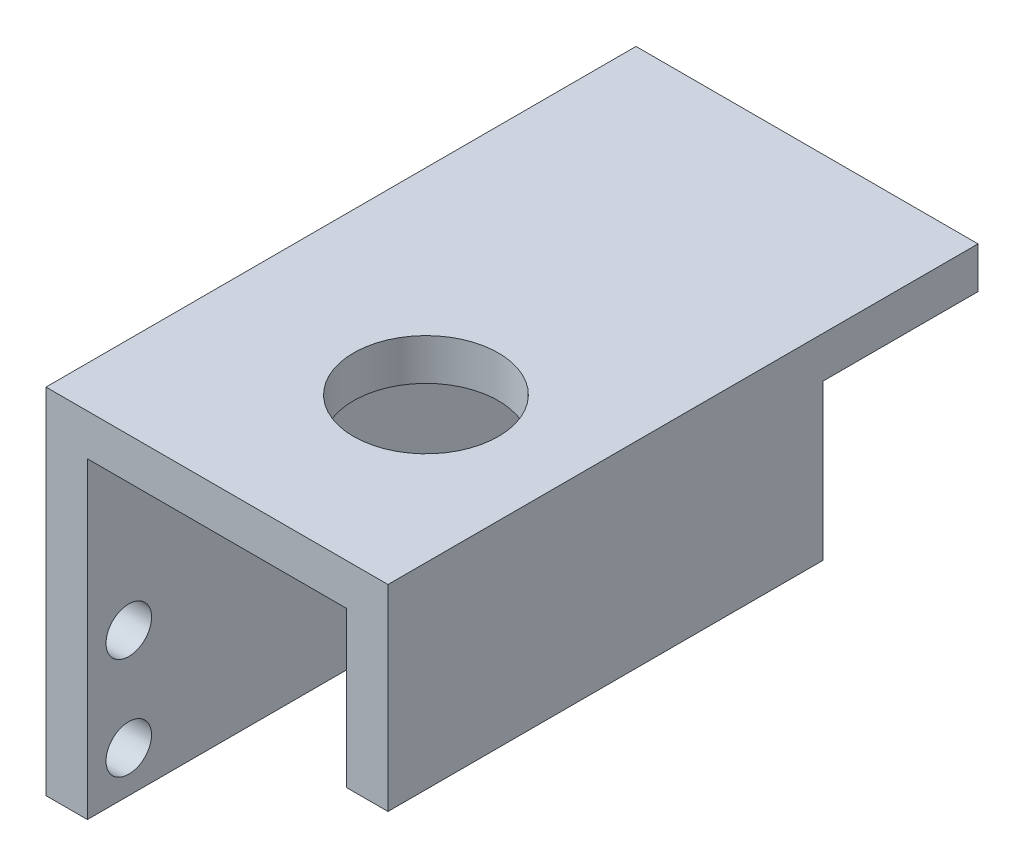
SolidWorks part; units mm, degrees
ref_plane "Front Plane" through (0, 0, 0) normal (0, 0, 1) x (1, 0, 0)
ref_plane "Top Plane" through (0, 0, 0) normal (0, 1, 0) x (1, 0, 0)
ref_plane "Right Plane" through (0, 0, 0) normal (1, 0, 0) x (0, 0, -1)
sketch "Sketch1" plane through (0, 0, 0) normal (1, 0, 0) x (0, 0, -1)
  line L1 (-28.51, 17.1) -> (28.51, 17.1)
  line L2 (-28.51, 17.1) -> (-28.51, -17.1)
  line L3 (-28.51, -17.1) -> (28.51, -17.1)
  line L4 (28.51, 17.1) -> (28.51, -17.1)
  line L5 (-28.51, 17.1) -> (28.51, -17.1) construction
  line L6 (-28.51, -17.1) -> (28.51, 17.1) construction
  circle A0 centre (-24.51, -3.25) radius 2.2
  circle A1 centre (-24.51, -13.1) radius 2.2
  circle A2 centre (24.51, -3.25) radius 2.2
  circle A3 centre (24.51, -13.1) radius 2.2
  point P0 (0, 0)
  dimension "D1" = 49.02
  dimension "D2" = 49.02
  dimension "D3" = 9.85
  dimension "D4" = 4.4
  dimension "D5" = 4.4
  dimension "D6" = 4.4
  dimension "D7" = 4.4
  dimension "D8" = 4
  dimension "D10" = 4
  dimension "D11" = 20.35
  dimension "D12" = 4
  dimension "D13" = 9.85
  dimension "D14" = 4
  dimension "D9" = 4
extrude "Boss-Extrude1" add sketch "Sketch1" along normal blind 4
sketch "Sketch2" plane through (4, 0, 0) normal (1, 0, 0) x (0, 0, -1)
  line L0 (28.51, -17.1) -> (28.51, 17.1) construction
  line L1 (-28.51, 17.1) -> (28.51, 17.1)
  line L2 (-28.51, 17.1) -> (-28.51, 13.1)
  line L3 (-28.51, 13.1) -> (28.51, 13.1)
  line L4 (28.51, 17.1) -> (28.51, 13.1)
  dimension "D1" = 4
extrude "Boss-Extrude2" add sketch "Sketch2" along normal blind 29.05
sketch "Sketch3" plane through (0, 13.1, 0) normal (0, -1, 0) x (1, 0, 0)
  line L0 (4, 28.51) -> (4, -28.51) construction
  line L1 (33.05, 28.51) -> (29.05, 28.51)
  line L2 (33.05, 28.51) -> (33.05, -13.51)
  line L3 (33.05, -13.51) -> (29.05, -13.51)
  line L4 (29.05, 28.51) -> (29.05, -13.51)
  line L5 (33.05, 28.51) -> (33.05, -28.51) construction
  line L7 (33.05, -28.51) -> (4, -28.51) construction
  line L8 (33.05, 28.51) -> (4, 28.51) construction
  point P5 (29.05, 28.51)
  point P11 (33.05, 28.51)
  dimension "D2" = 15
  dimension "D3" = 25.05
extrude "Boss-Extrude3" add sketch "Sketch3" along normal blind 15
sketch "Sketch5" plane through (0, 17.1, 0) normal (0, 1, 0) x (1, 0, 0)
  line L0 (0, 28.51) -> (0, -28.51) construction
  line L1 (33.05, -28.51) -> (0, -28.51) construction
  circle A0 centre (19, -10.79) radius 7
  dimension "D2" = 17.72
  dimension "D3" = 14
  dimension "D1" = 19
extrude "Cut-Extrude1" cut sketch "Sketch5" against normal up to surface (4 mm away) up to face at (22.0333, 13.1, -4.5033)
